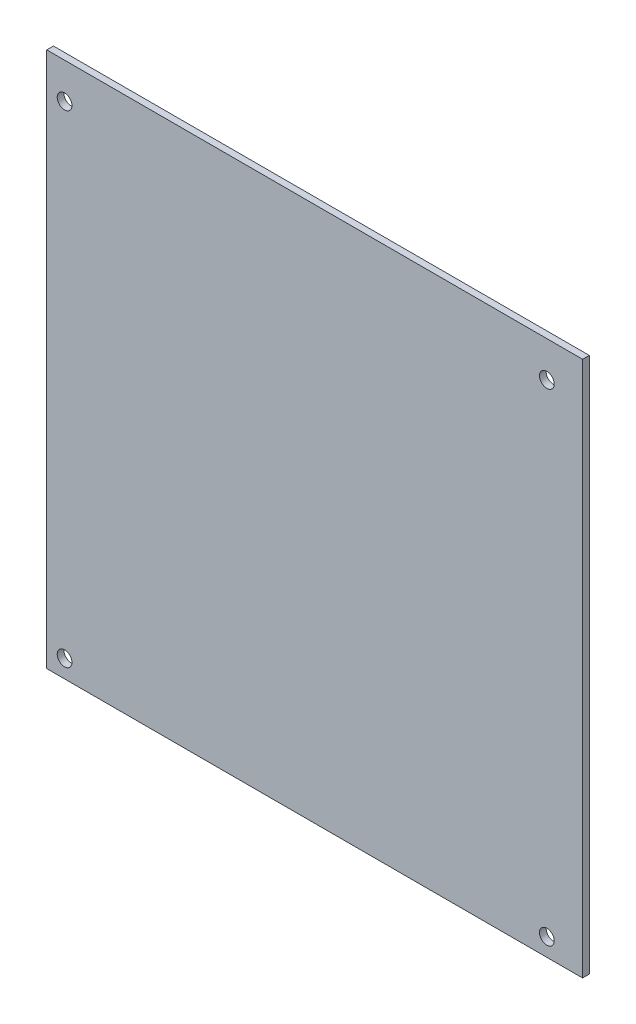
SolidWorks part; units mm, degrees
ref_plane "Спереди" through (0, 0, 0) normal (0, 0, 1) x (1, 0, 0)
ref_plane "Сверху" through (0, 0, 0) normal (0, 1, 0) x (1, 0, 0)
ref_plane "Справа" through (0, 0, 0) normal (1, 0, 0) x (0, 0, -1)
sketch "Эскиз1" plane through (0, 0, 0) normal (0, 0, 1) x (1, 0, 0)
  line L1 (0, 0) -> (120, 0)
  line L2 (0, 0) -> (0, 120)
  line L3 (0, 120) -> (120, 120)
  line L4 (120, 0) -> (120, 120)
  circle A0 centre (4, 4) radius 1.65
  circle A1 centre (112, 4) radius 1.65
  circle A2 centre (4, 112) radius 1.65
  circle A3 centre (112, 112) radius 1.65
  dimension "D5" = 108
  dimension "D6" = 108
  dimension "D7" = 3.3
  dimension "D1" = 120
  dimension "D2" = 120
  dimension "D3" = 4
  dimension "D4" = 4
extrude "Бобышка-Вытянуть1" add sketch "Эскиз1" along normal blind 1.5
